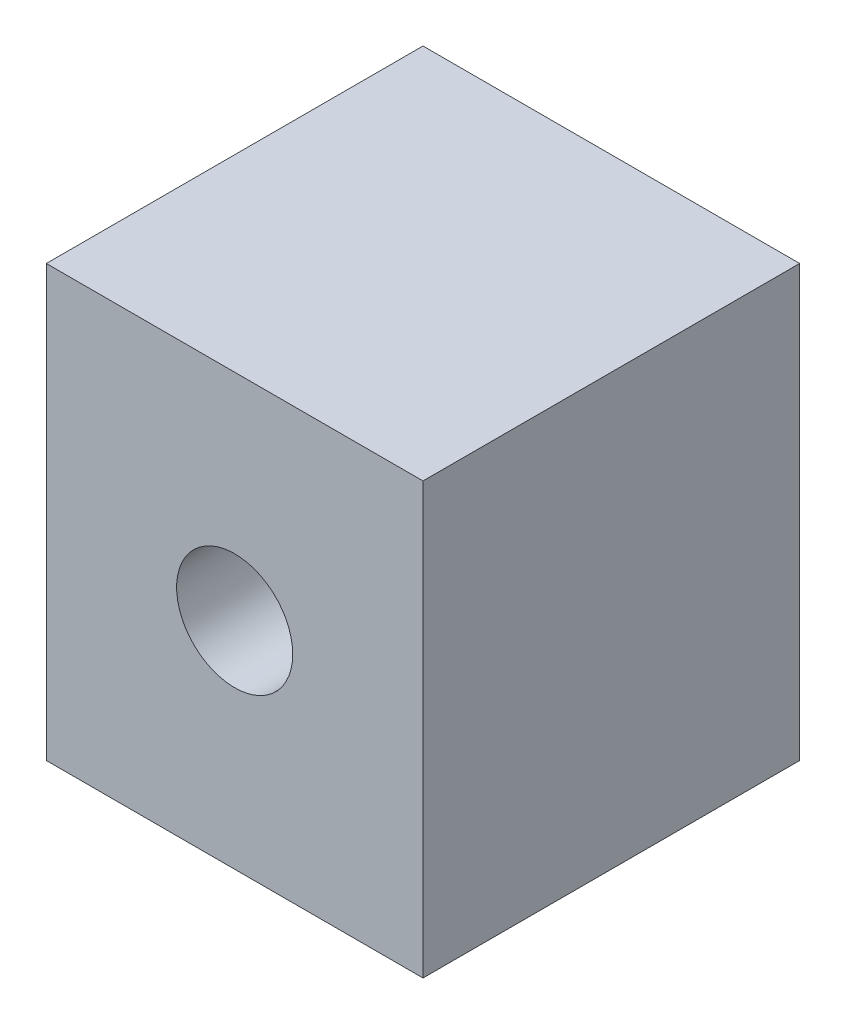
SolidWorks part; units mm, degrees
ref_plane "Front Plane" through (0, 0, 0) normal (0, 0, 1) x (1, 0, 0)
ref_plane "Top Plane" through (0, 0, 0) normal (0, 1, 0) x (1, 0, 0)
ref_plane "Right Plane" through (0, 0, 0) normal (1, 0, 0) x (0, 0, -1)
sketch "Sketch2" plane through (0, 0, 0) normal (0, 1, 0) x (1, 0, 0)
  line L1 (0, 0) -> (44.45, 0)
  line L2 (0, 0) -> (0, -44.45)
  line L3 (0, -44.45) -> (44.45, -44.45)
  line L4 (44.45, 0) -> (44.45, -44.45)
extrude "Boss-Extrude1" add sketch "Sketch2" along normal blind 50.8
sketch "Sketch3" plane through (0, 0, 44.45) normal (0, 0, 1) x (1, 0, 0)
  circle A0 centre (22.225, 25.4) radius 6.85
  dimension "D1" = 13.7
extrude "Cut-Extrude1" cut sketch "Sketch3" against normal blind 50.8
sketch "Sketch4" plane through (0, 0, 0) normal (0, -1, 0) x (1, 0, 0)
  circle A0 centre (11.0818, 22.225) radius 3.675
  circle A1 centre (33.401, 22.225) radius 3.675
  dimension "D1" = 7.35
  dimension "D2" = 7.35
extrude "Cut-Extrude2" cut sketch "Sketch4" against normal blind 6.35
